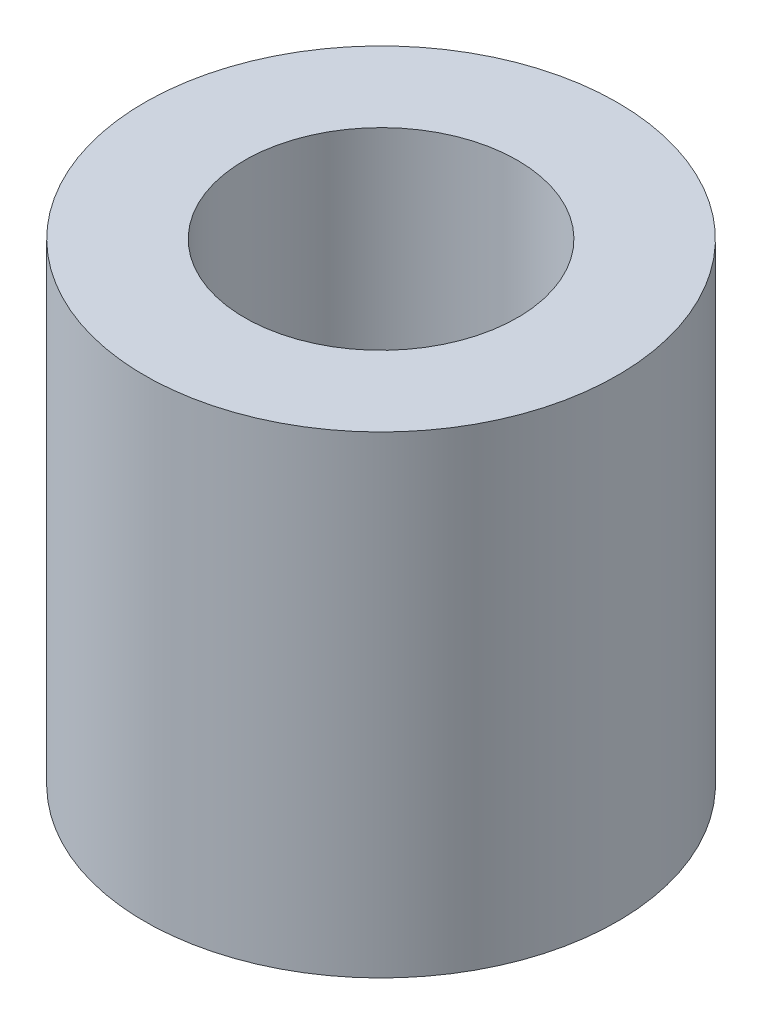
SolidWorks part; units mm, degrees
ref_plane "Front Plane" through (0, 0, 0) normal (0, 0, 1) x (1, 0, 0)
ref_plane "Top Plane" through (0, 0, 0) normal (0, 1, 0) x (1, 0, 0)
ref_plane "Right Plane" through (0, 0, 0) normal (1, 0, 0) x (0, 0, -1)
sketch "Sketch2" plane through (0, 0, 0) normal (0, 0, 1) x (1, 0, 0)
  line L0 (0, 0) -> (0, 9.525) construction
  line L1 (3.175, -10.3187) -> (10.3187, -10.3187)
  line L2 (3.175, -10.3187) -> (3.175, 10.3187)
  line L3 (3.175, 10.3187) -> (10.3187, 10.3187)
  line L4 (10.3187, -10.3187) -> (10.3187, 10.3187)
  line L6 (3.175, 10.3187) -> (5.9531, 10.3187)
  line L7 (3.175, 10.3187) -> (3.175, -0.7938)
  line L8 (3.175, -0.7938) -> (5.9531, -0.7937)
  line L9 (5.9531, 10.3187) -> (5.9531, -0.7937)
  point P8 (3.175, 0)
  dimension "D1" = 10.3187
  dimension "D2" = 3.175
  dimension "D3" = 20.6375
  dimension "D4" = 5.9531
  dimension "D5" = 9.525
revolve "Revolve1" add sketch "Sketch2" angle 360 about L0
